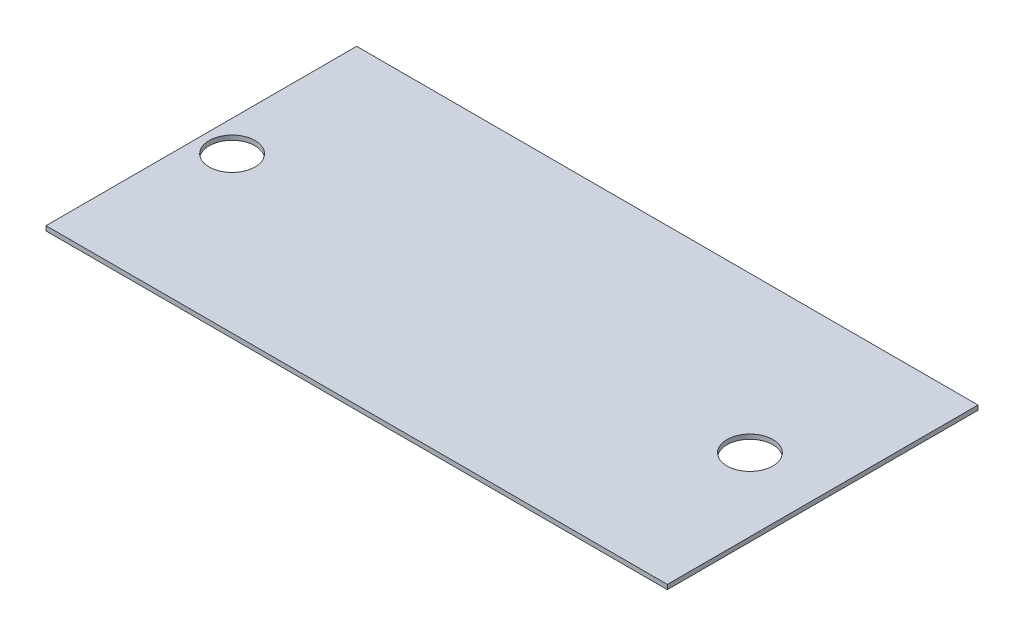
SolidWorks part; units mm, degrees
ref_plane "Front Plane" through (0, 0, 0) normal (0, 0, 1) x (1, 0, 0)
ref_plane "Top Plane" through (0, 0, 0) normal (0, 1, 0) x (1, 0, 0)
ref_plane "Right Plane" through (0, 0, 0) normal (1, 0, 0) x (0, 0, -1)
sketch "Sketch1" plane through (0, 0, 0) normal (0, 1, 0) x (1, 0, 0)
  line L1 (0, 0) -> (406.4, 0)
  line L2 (0, 0) -> (0, 203.2)
  line L3 (0, 203.2) -> (406.4, 203.2)
  line L4 (406.4, 0) -> (406.4, 203.2)
  dimension "D1" = 406.4
  dimension "D2" = 203.2
extrude "Boss-Extrude1" add sketch "Sketch1" along normal blind 3
sketch "Sketch2" plane through (0, 3, 0) normal (0, 1, 0) x (1, 0, 0)
  line L0 (406.4, 0) -> (406.4, 203.2) construction
  circle A0 centre (20.1228, 101.6) radius 15
  circle A1 centre (358.831, 101.6) radius 15
  point P6 (406.4, 101.6)
  dimension "D1" = 30
  dimension "D2" = 30
extrude "Cut-Extrude1" cut sketch "Sketch2" against normal through all
